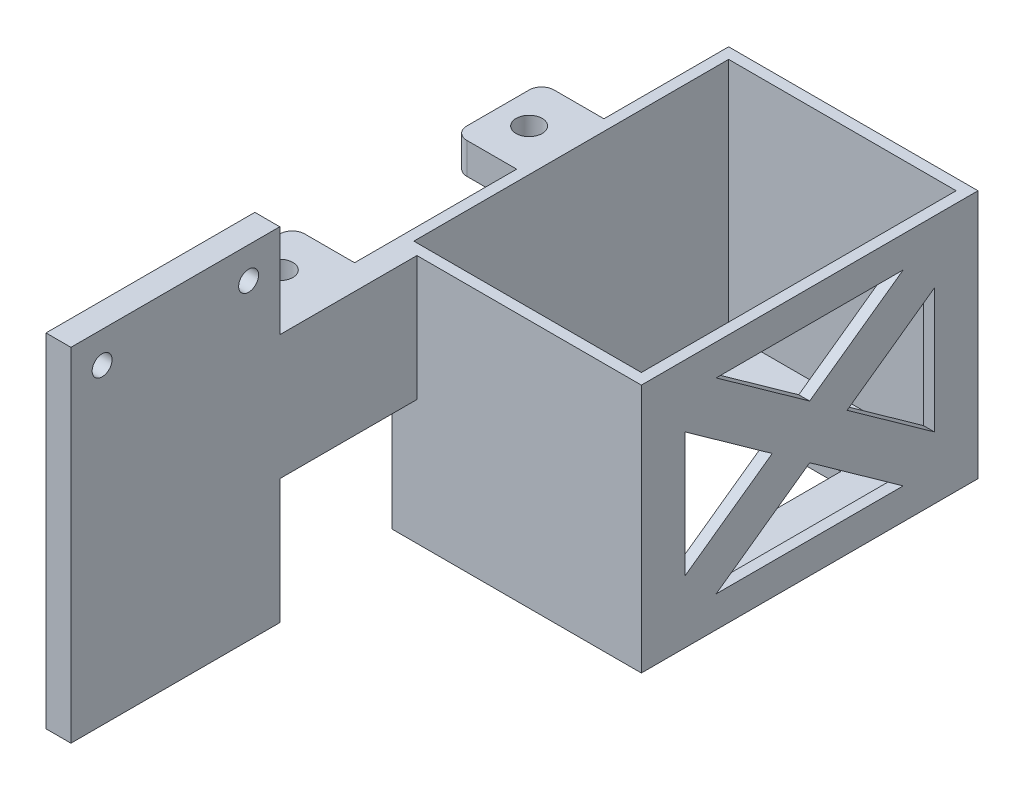
SolidWorks part; units mm, degrees
ref_plane "Front Plane" through (0, 0, 0) normal (0, 0, 1) x (1, 0, 0)
ref_plane "Top Plane" through (0, 0, 0) normal (0, 1, 0) x (1, 0, 0)
ref_plane "Right Plane" through (0, 0, 0) normal (1, 0, 0) x (0, 0, -1)
sketch "Sketch1" plane through (0, 0, 0) normal (0, 1, 0) x (1, 0, 0)
  line L1 (109.4484, -179.3604) -> (119.4484, -179.3604)
  line L2 (109.4484, -179.3604) -> (109.4484, -165.3604)
  line L3 (109.4484, -165.3604) -> (119.4484, -165.3604)
  line L4 (119.4484, -179.3604) -> (119.4484, -165.3604)
  line L5 (109.4484, -179.3604) -> (119.4484, -165.3604) construction
  line L6 (109.4484, -165.3604) -> (119.4484, -179.3604) construction
  line L8 (109.4484, -125.3604) -> (119.4484, -125.3604)
  line L9 (109.4484, -125.3604) -> (109.4484, -139.3604)
  line L10 (109.4484, -139.3604) -> (119.4484, -139.3604)
  line L11 (119.4484, -125.3604) -> (119.4484, -139.3604)
  line L12 (109.4484, -125.3604) -> (119.4484, -139.3604) construction
  line L13 (109.4484, -139.3604) -> (119.4484, -125.3604) construction
  circle A0 centre (114.4484, -172.3604) radius 2.1
  circle A1 centre (114.4484, -132.3604) radius 2.1
  point P0 (114.4484, -172.3604)
  point P8 (114.4484, -132.3604)
  dimension "D1" = 7
  dimension "D2" = 14
sketch "Sketch2" plane through (0, 0, 0) normal (0, 1, 0) x (1, 0, 0)
  line L1 (109.4484, -125.3604) -> (119.4484, -125.3604)
  line L2 (109.4484, -125.3604) -> (109.4484, -139.3604)
  line L3 (109.4484, -139.3604) -> (119.4484, -139.3604)
  line L4 (119.4484, -125.3604) -> (119.4484, -139.3604)
  line L5 (109.4484, -165.3604) -> (119.4484, -165.3604)
  line L6 (109.4484, -165.3604) -> (109.4484, -179.3604)
  line L7 (109.4484, -179.3604) -> (119.4484, -179.3604)
  line L8 (119.4484, -165.3604) -> (119.4484, -179.3604)
  circle A0 centre (114.4484, -132.3604) radius 2.1
  circle A1 centre (114.4484, -172.3604) radius 2.1
extrude "Boss-Extrude1" add sketch "Sketch2" along normal blind 5 contours L6 L5 L8 L7 | L2 L1 L4 L3 | A1 | A0
sketch "Sketch3" plane through (119.4484, 0, 0) normal (1, 0, 0) x (0, 0, -1)
  line L0 (-179.3604, 5) -> (-125.3604, 5) construction
  line L1 (-107.8604, 5) -> (-107.8604, -34)
  line L2 (-107.8604, 5) -> (-196.8604, 5)
  line L3 (-152.3604, 5) -> (-152.3604, -34)
  line L4 (-107.8604, -34) -> (-196.8604, -34)
  line L5 (-196.8604, 5) -> (-196.8604, -34)
  line M6 (-179.3604, 0) -> (-165.3604, 0)
  line M7 (-165.3604, 0) -> (-165.3604, 5)
  line M8 (-165.3604, 5) -> (-179.3604, 5)
  line M9 (-179.3604, 5) -> (-179.3604, 0)
  dimension "D1" = 39
  dimension "D2" = 44.5
extrude "Boss-Extrude2" add sketch "Sketch3" along normal blind 2 contours L2 L5 L4 L3 M7 M6 M9 | L4 L1 L2 L3 | M9 M6 M7 M8
sketch "Sketch4" plane through (121.4484, 0, 0) normal (1, 0, 0) x (0, 0, -1)
  line L0 (-107.8604, -34) -> (-196.8604, -34) construction
  line L1 (-196.8604, 5) -> (-194.8604, 5)
  line L2 (-196.8604, 5) -> (-196.8604, -34)
  line L3 (-196.8604, -34) -> (-194.8604, -34)
  line L4 (-194.8604, 5) -> (-194.8604, -34)
  line L5 (-152.3604, 5) -> (-152.3604, -34) construction
  line L6 (-107.8604, 5) -> (-196.8604, 5) construction
  line L7 (-107.8604, -34) -> (-109.8604, -34)
  line L8 (-109.8604, 5) -> (-109.8604, -34)
  line L9 (-107.8604, 5) -> (-109.8604, 5)
  line L10 (-107.8604, 5) -> (-107.8604, -34)
  line L13 (-194.8604, 5) -> (-194.8604, 3)
  line L15 (-109.8604, 5) -> (-109.8604, 3)
  line L16 (-194.8604, -34) -> (-109.8604, -34)
  line L17 (-194.8604, -34) -> (-194.8604, -32)
  line L18 (-194.8604, -32) -> (-109.8604, -32)
  line L19 (-109.8604, -34) -> (-109.8604, -32)
  line M6 (-107.8604, -34) -> (-107.8604, 5)
  line M7 (-107.8604, 5) -> (-196.8604, 5)
  line M8 (-196.8604, 5) -> (-196.8604, -34)
  line M9 (-196.8604, -34) -> (-107.8604, -34)
  dimension "D1" = 2
  dimension "D2" = 2
  dimension "D3" = 2
extrude "Boss-Extrude4" add sketch "Sketch4" along normal blind 32 contours L5 L18 L4 M9 | L18 L5 L16 L8 | L8 M7 M9 M6 | L4 M7 M8 M9
sketch "Sketch5" plane through (0, -32, 0) normal (0, 1, 0) x (1, 0, 0)
  line L0 (153.4484, -194.8604) -> (121.4484, -194.8604) construction
  line L1 (153.4484, -109.8604) -> (151.4484, -109.8604)
  line L2 (153.4484, -109.8604) -> (153.4484, -194.8604)
  line L3 (153.4484, -194.8604) -> (151.4484, -194.8604)
  line L4 (151.4484, -109.8604) -> (151.4484, -194.8604)
  dimension "D1" = 2
extrude "Boss-Extrude5" add sketch "Sketch5" along normal up to surface (37 mm away) up to face at (125.6984, 5, 152.3604)
sketch "Sketch6" plane through (0, 0, 196.8604) normal (0, 0, 1) x (1, 0, 0)
  line L0 (153.4484, 5) -> (119.4484, 5) construction
  line L1 (129.4484, 5) -> (143.4484, 5)
  line L2 (129.4484, 5) -> (129.4484, -25)
  line L3 (129.4484, -25) -> (143.4484, -25)
  line L4 (143.4484, 5) -> (143.4484, -25)
  line L5 (153.4484, 5) -> (153.4484, -34) construction
  line L6 (119.4484, 5) -> (119.4484, -34) construction
  dimension "D1" = 10
  dimension "D2" = 10
  dimension "D3" = 30
extrude "Cut-Extrude1" cut sketch "Sketch6" against normal blind 200
sketch "Sketch7" plane through (153.4484, 0, 0) normal (1, 0, 0) x (0, 0, -1)
  line L0 (-196.8604, -14.5) -> (-107.8604, -14.5) construction
  line L1 (-196.8604, 5) -> (-196.8604, -34) construction
  line L2 (-107.8604, -34) -> (-107.8604, 5) construction
  line L4 (-189.3604, -24.5) -> (-169.3604, -24.5)
  line L5 (-189.3604, -24.5) -> (-189.3604, -4.5)
  line L6 (-189.3604, -4.5) -> (-169.3604, -4.5)
  line L7 (-169.3604, -24.5) -> (-169.3604, -4.5)
  line L8 (-189.3604, -24.5) -> (-169.3604, -4.5) construction
  line L9 (-189.3604, -4.5) -> (-169.3604, -24.5) construction
  line L10 (-162.3604, -24.5) -> (-142.3604, -24.5)
  line L11 (-162.3604, -24.5) -> (-162.3604, -4.5)
  line L12 (-162.3604, -4.5) -> (-142.3604, -4.5)
  line L13 (-142.3604, -24.5) -> (-142.3604, -4.5)
  line L14 (-162.3604, -24.5) -> (-142.3604, -4.5) construction
  line L15 (-162.3604, -4.5) -> (-142.3604, -24.5) construction
  line L16 (-135.3604, -24.5) -> (-115.3604, -24.5)
  line L17 (-135.3604, -24.5) -> (-135.3604, -4.5)
  line L18 (-135.3604, -4.5) -> (-115.3604, -4.5)
  line L19 (-115.3604, -24.5) -> (-115.3604, -4.5)
  line L20 (-135.3604, -24.5) -> (-115.3604, -4.5) construction
  line L21 (-135.3604, -4.5) -> (-115.3604, -24.5) construction
  point P6 (-179.3604, -14.5)
  point P11 (-152.3604, -14.5)
  point P16 (-125.3604, -14.5)
  dimension "D1" = 7
  dimension "D2" = 20
  dimension "D3" = 20
  dimension "D4" = 20
  dimension "D5" = 20
  dimension "D6" = 20
  dimension "D7" = 20
  dimension "D8" = 7.5
extrude "Cut-Extrude2" cut sketch "Sketch7" against normal blind 16
fillet "Fillet1" radius 2 4 edges at (109.4484, 2.5, 125.3604) (109.4484, 2.5, 139.3604) (109.4484, 2.5, 165.3604) (109.4484, 2.5, 179.3604)
sketch "Sketch8" plane through (153.4484, 0, 0) normal (1, 0, 0) x (0, 0, -1)
  line L1 (-200.7189, -38.4244) -> (-104.7996, -38.4244)
  line L2 (-200.7189, -38.4244) -> (-200.7189, 8.239)
  line L3 (-200.7189, 8.239) -> (-104.7996, 8.239)
  line L4 (-104.7996, -38.4244) -> (-104.7996, 8.239)
  line L5 (-200.7189, -38.4244) -> (-104.7996, 8.239) construction
  line L6 (-200.7189, 8.239) -> (-104.7996, -38.4244) construction
  point P0 (-152.7592, -15.0927)
extrude "Cut-Extrude4" cut sketch "Sketch8" against normal up to surface (34 mm away) up to face at (119.4484, -3.1667, 152.3604)
sketch "Sketch9" plane through (119.4484, 0, 0) normal (1, 0, 0) x (0, 0, -1)
  line L0 (-132.3604, 5) -> (-132.3604, -35) construction
  line L1 (-125.3604, 5) -> (-139.3604, 5) construction
  line L2 (-157.3604, -35) -> (-157.3604, 5)
  line L3 (-157.3604, -35) -> (-107.3604, -35)
  line L4 (-132.3604, -35) -> (-132.3604, 5)
  line L5 (-157.3604, 5) -> (-107.3604, 5)
  line L6 (-107.3604, -35) -> (-107.3604, 5)
  line M7 (-139.3604, 5) -> (-139.3604, 0)
  line M8 (-139.3604, 0) -> (-125.3604, 0)
  line M9 (-125.3604, 0) -> (-125.3604, 5)
  line M10 (-125.3604, 5) -> (-139.3604, 5)
  dimension "D1" = 40
  dimension "D2" = 25
extrude "Boss-Extrude6" add sketch "Sketch9" along normal blind 2 contours L3 L6 L5 L4 M9 M8 | L5 L2 L3 L4 M8 M7 | L4 M8 M10 M7 | L4 M8 M9 M10
sketch "Sketch11" plane through (121.4484, 0, 0) normal (1, 0, 0) x (0, 0, -1)
  line L1 (-157.3604, 5) -> (-159.3604, 5)
  line L2 (-157.3604, 5) -> (-157.3604, -35)
  line L3 (-157.3604, -35) -> (-159.3604, -35)
  line L4 (-159.3604, 5) -> (-159.3604, -35)
  line L5 (-107.3604, 5) -> (-105.3604, 5)
  line L6 (-107.3604, 5) -> (-107.3604, -35)
  line L7 (-107.3604, -35) -> (-105.3604, -35)
  line L8 (-105.3604, 5) -> (-105.3604, -35)
  line L9 (-157.3604, -35) -> (-107.3604, -35)
  line L10 (-157.3604, -35) -> (-157.3604, -33)
  line L11 (-157.3604, -33) -> (-107.3604, -33)
  line L12 (-107.3604, -35) -> (-107.3604, -33)
  line M4 (-157.3604, 5) -> (-157.3604, -35)
  line M6 (-107.3604, -35) -> (-107.3604, 5)
  dimension "D1" = 2
  dimension "D2" = 2
  dimension "D3" = 2
extrude "Boss-Extrude9" add sketch "Sketch11" along normal blind 36 separate body contours L1 L4 L3 L2 M4 | L8 L5 L6 L7 M6
sketch "Sketch12" plane through (121.4484, 0, 0) normal (1, 0, 0) x (0, 0, -1)
  line L0 (-107.3604, -35) -> (-107.3604, 5) construction
  line L1 (-157.3604, -35) -> (-107.3604, -35)
  line L2 (-157.3604, -35) -> (-157.3604, -33)
  line L3 (-157.3604, -33) -> (-107.3604, -33)
  line L4 (-107.3604, -35) -> (-107.3604, -33)
  dimension "D1" = 2
extrude "Cut-Extrude5" cut sketch "Sketch12" against normal blind 36
sketch "Sketch13" plane through (121.4484, 0, 0) normal (1, 0, 0) x (0, 0, -1)
  line L1 (-157.3604, -33) -> (-107.3604, -33)
  line L2 (-157.3604, -33) -> (-157.3604, -35)
  line L3 (-157.3604, -35) -> (-107.3604, -35)
  line L4 (-107.3604, -33) -> (-107.3604, -35)
extrude "Boss-Extrude11" add sketch "Sketch13" along normal blind 36
sketch "Sketch14" plane through (121.4484, 0, 0) normal (-1, 0, 0) x (0, 0, 1)
  line L0 (107.3604, 5) -> (105.3604, 5)
  line L1 (105.3604, 5) -> (105.3604, -35)
  line L2 (105.3604, -35) -> (159.3604, -35)
  line L3 (159.3604, -35) -> (159.3604, 5)
  line L4 (159.3604, 5) -> (157.3604, 5)
  line L5 (157.3604, 5) -> (157.3604, -33)
  line L6 (157.3604, -33) -> (107.3604, -33)
  line L7 (107.3604, -33) -> (107.3604, 5)
extrude "Boss-Extrude12" add sketch "Sketch14" along normal up to surface (2 mm away) up to face at (119.4484, -5.75, 132.3604)
sketch "Sketch15" plane through (157.4484, 0, 0) normal (1, 0, 0) x (0, 0, -1)
  line L1 (-159.3604, 5) -> (-105.3604, 5)
  line L2 (-159.3604, 5) -> (-159.3604, -35)
  line L3 (-159.3604, -35) -> (-105.3604, -35)
  line L4 (-105.3604, 5) -> (-105.3604, -35)
extrude "Boss-Extrude13" add sketch "Sketch15" along normal blind 2
sketch "Sketch16" plane through (159.4484, 0, 0) normal (1, 0, 0) x (0, 0, -1)
  line L0 (-132.3604, 5) -> (-132.3604, -35) construction
  line L1 (-105.3604, 5) -> (-159.3604, 5) construction
  line L2 (-159.3604, -35) -> (-105.3604, -35) construction
  line L3 (-159.3604, -15) -> (-105.3604, -15) construction
  line L4 (-159.3604, 5) -> (-159.3604, -35) construction
  line L5 (-105.3604, -35) -> (-105.3604, 5) construction
  line L6 (-152.3604, -5) -> (-117.3604, -30)
  line L7 (-152.3604, -30) -> (-112.3604, -30)
  line L8 (-152.3604, -30) -> (-152.3604, 0)
  line L9 (-152.3604, 0) -> (-112.3604, 0)
  line L10 (-112.3604, -30) -> (-112.3604, 0)
  line L11 (-152.3604, -30) -> (-112.3604, 0) construction
  line L12 (-152.3604, 0) -> (-112.3604, -30) construction
  line L13 (-147.3604, 0) -> (-112.3604, -25)
  line L14 (-152.3604, -25) -> (-117.3604, 0)
  line L15 (-147.3604, -30) -> (-112.3604, -5)
  point P12 (-132.3604, -15)
  dimension "D1" = 30
  dimension "40" = 40
  dimension "D2" = 5
  dimension "D3" = 5
  dimension "D4" = 5
  dimension "D5" = 5
  dimension "D6" = 5
  dimension "D7" = 5
  dimension "D8" = 5
  dimension "D9" = 5
extrude "Cut-Extrude6" cut sketch "Sketch16" against normal blind 2 contours L8 L14 L6 | L13 L14 L9 | L15 L13 L10 | L15 L7 L6
sketch "Sketch17" plane through (119.4484, 0, 0) normal (1, 0, 0) x (0, 0, -1)
  line L1 (-159.3604, 5) -> (-214.3604, 5)
  line L2 (-159.3604, 5) -> (-159.3604, -32)
  line L3 (-159.3604, -32) -> (-214.3604, -32)
  line L4 (-214.3604, 5) -> (-214.3604, -32)
  dimension "D1" = 55
  dimension "D2" = 37
extrude "Boss-Extrude14" add sketch "Sketch17" along normal blind 4
sketch "Sketch18" plane through (123.4484, 0, 0) normal (1, 0, 0) x (0, 0, -1)
  line L0 (-214.3604, -13.5) -> (-159.3604, -13.5) construction
  line L3 (-186.8604, 5) -> (-186.8604, -33.1525) construction
  line L8 (-214.3604, 5) -> (-214.3604, -32) construction
  line L9 (-159.3604, -32) -> (-159.3604, 5) construction
  circle A0 centre (-209.3604, -1.75) radius 1.6
  circle A1 centre (-209.3604, -25.25) radius 1.6
  circle A4 centre (-164.3604, -25.25) radius 1.6
  circle A5 centre (-164.3604, -1.75) radius 1.6
  point P6 (-200.6104, -13.5)
  dimension "D2" = 3.2
  dimension "D3" = 3.2
  dimension "D4" = 22.5
  dimension "D5" = 11.75
  dimension "D6" = 11.75
  dimension "D1" = 22.5
extrude "Cut-Extrude7" cut sketch "Sketch18" against normal blind 11
sketch "Sketch19" plane through (119.4484, 0, 0) normal (-1, 0, 0) x (0, 0, 1)
  circle A0 centre (164.3604, -1.75) radius 1.6
extrude "Boss-Extrude15" add sketch "Sketch19" against normal up to surface (4 mm away) up to face at (123.4484, -25.25, 207.7604)
sketch "Sketch20" plane through (119.4484, 0, 0) normal (-1, 0, 0) x (0, 0, 1)
  circle A0 centre (209.3604, -1.75) radius 3.6
  circle A1 centre (209.3604, -25.25) radius 3.6
  circle A2 centre (164.3604, -25.25) radius 3.6
  dimension "D1" = 7.2
  dimension "D2" = 7.2
  dimension "D3" = 7.2
extrude "Cut-Extrude8" cut sketch "Sketch20" against normal blind 2.2 contours A0 | A1 | A2
sketch "Sketch21" plane through (123.4484, 0, 0) normal (1, 0, 0) x (0, 0, -1)
  line L1 (-159.3604, -32) -> (-216.2773, -32)
  line L2 (-159.3604, -32) -> (-159.3604, 7.408)
  line L3 (-159.3604, 7.408) -> (-216.2773, 7.408)
  line L4 (-216.2773, -32) -> (-216.2773, 7.408)
extrude "Cut-Extrude9" cut sketch "Sketch21" against normal up to surface (4 mm away) up to face at (119.4484, -1.75, 212.9604)
sketch "Sketch22" plane through (119.4484, 0, 0) normal (1, 0, 0) x (0, 0, -1)
  line L0 (-189.3604, 20) -> (-189.3604, -7.5)
  line L1 (-189.3604, 20) -> (-226.8604, 20)
  line L4 (-226.8604, 20) -> (-226.8604, -7.5)
  line L7 (-208.1104, 20) -> (-208.1104, -7.5) construction
  line L8 (-208.1104, -7.5) -> (-189.3604, -7.5) construction
  line L9 (-226.8604, -7.5) -> (-189.3604, -7.5)
  circle A0 centre (-219.8604, 15) radius 1.6
  circle A1 centre (-196.3604, 15) radius 1.6
  dimension "D4" = 3.2
  dimension "D5" = 3.2
  dimension "D6" = 11.75
  dimension "D7" = 11.75
  dimension "D8" = 22.5
  dimension "D9" = 22.5
  dimension "D3" = 37.5
extrude "Boss-Extrude16" add sketch "Sketch22" along normal blind 2 separate body
sketch "Sketch23" plane through (119.4484, 0, 0) normal (1, 0, 0) x (0, 0, -1)
  line L1 (-159.3604, 5) -> (-189.3604, 5)
  line L2 (-159.3604, 5) -> (-159.3604, -7.5)
  line L3 (-159.3604, -7.5) -> (-189.3604, -7.5)
  line L4 (-189.3604, 5) -> (-189.3604, -7.5)
extrude "Boss-Extrude17" add sketch "Sketch23" along normal blind 2
sketch "Sketch25" plane through (0, -35, 0) normal (0, -1, 0) x (-1, 0, 0)
  line L0 (-139.4484, -159.3604) -> (-139.4484, -105.3604) construction
  line L1 (-119.4484, -159.3604) -> (-159.4484, -159.3604) construction
  line L2 (-119.4484, -105.3604) -> (-159.4484, -105.3604) construction
  line L4 (-129.4484, -117.3604) -> (-149.4484, -117.3604)
  line L5 (-129.4484, -117.3604) -> (-129.4484, -147.3604)
  line L6 (-129.4484, -147.3604) -> (-149.4484, -147.3604)
  line L7 (-149.4484, -117.3604) -> (-149.4484, -147.3604)
  line L8 (-129.4484, -117.3604) -> (-149.4484, -147.3604) construction
  line L9 (-129.4484, -147.3604) -> (-149.4484, -117.3604) construction
  point P6 (-139.4484, -132.3604)
  dimension "D1" = 20
  dimension "D2" = 30
extrude "Cut-Extrude10" cut sketch "Sketch25" against normal blind 15
sketch "Sketch26" plane through (121.4484, 0, 0) normal (1, 0, 0) x (0, 0, -1)
  line L1 (-189.3604, 20) -> (-226.8604, 20)
  line L2 (-189.3604, 20) -> (-189.3604, 5)
  line L4 (-226.8604, 20) -> (-226.8604, -7.5)
  line L5 (-189.3604, 5) -> (-159.3604, 5)
  line L7 (-189.3604, -7.5) -> (-159.3604, -7.5)
  line L8 (-159.3604, 5) -> (-159.3604, -7.5)
  line L9 (-189.3604, -35) -> (-226.8604, -35)
  line L10 (-159.3604, -35) -> (-159.3604, -7.5)
  line L11 (-159.3604, -7.5) -> (-189.3604, -7.5)
  line L12 (-226.8604, -35) -> (-226.8604, -7.5)
  line L13 (-189.3604, -7.5) -> (-159.3604, -7.5)
  line L14 (-189.3604, -7.5) -> (-189.3604, -35)
  line L16 (-159.3604, -7.5) -> (-159.3604, -35)
  circle A0 centre (-219.8604, 15) radius 1.6
  circle A1 centre (-196.3604, 15) radius 1.6
  line M1 (-159.3604, -7.5) -> (-159.3604, 5)
  line M2 (-159.3604, 5) -> (-189.3604, 5)
  line M3 (-189.3604, 5) -> (-189.3604, 20)
  line M4 (-189.3604, 20) -> (-226.8604, 20)
  line M5 (-226.8604, 20) -> (-226.8604, -7.5)
  line M6 (-226.8604, -7.5) -> (-159.3604, -7.5)
  circle M7 centre (-219.8604, 15) radius 1.6
  circle M8 centre (-196.3604, 15) radius 1.6
extrude "Boss-Extrude18" add sketch "Sketch26" along normal blind 2 contours M6 M1 M2 M3 M4 M5 M7 M8 | L14 L12 L9 M6
sketch "Sketch27" plane through (121.4484, 0, 0) normal (-1, 0, 0) x (0, 0, 1)
  line L1 (189.3604, -7.5) -> (226.8604, -7.5)
  line L2 (189.3604, -7.5) -> (189.3604, -35)
  line L3 (189.3604, -35) -> (226.8604, -35)
  line L4 (226.8604, -7.5) -> (226.8604, -35)
extrude "Boss-Extrude19" add sketch "Sketch27" along normal up to surface (2 mm away) up to face at (119.4484, -0.9375, 161.2979)
sketch "Sketch28" plane through (0, 5, 0) normal (0, 1, 0) x (1, 0, 0)
  line L0 (139.4484, -107.3604) -> (139.4484, -157.3604) construction
  line L1 (157.4484, -107.3604) -> (121.4484, -107.3604) construction
  line L2 (157.4484, -157.3604) -> (121.4484, -157.3604) construction
  line L4 (121.1984, -157.6104) -> (157.6984, -157.6104)
  line L5 (121.1984, -157.6104) -> (121.1984, -107.1104)
  line L6 (121.1984, -107.1104) -> (157.6984, -107.1104)
  line L7 (157.6984, -157.6104) -> (157.6984, -107.1104)
  line L8 (121.1984, -157.6104) -> (157.6984, -107.1104) construction
  line L9 (121.1984, -107.1104) -> (157.6984, -157.6104) construction
  point P6 (139.4484, -132.3604)
  dimension "D1" = 50.5
  dimension "D2" = 36.5
extrude "Cut-Extrude11" cut sketch "Sketch28" against normal up to surface (38 mm away) up to face at (139.4484, -33, 132.3604)
sketch "Sketch29" plane through (123.4484, 0, 0) normal (1, 0, 0) x (0, 0, -1)
  line L0 (-219.8604, 15) -> (-209.8604, 15) construction
  line L1 (-196.3604, 15) -> (-186.3604, 15)
  line L3 (-189.3604, 20) -> (-226.8604, 20) construction
  line L4 (-214.8604, 20) -> (-181.3604, 20)
  line L5 (-214.8604, 20) -> (-214.8604, -35)
  line L6 (-214.8604, -35) -> (-181.3604, -35)
  line L7 (-181.3604, 20) -> (-181.3604, -35)
  circle A0 centre (-186.3604, 15) radius 1.6
  circle A1 centre (-209.8604, 15) radius 1.6
  dimension "D3" = 3.2
  dimension "D4" = 3.2
  dimension "D6" = 5
  dimension "D1" = 10
  dimension "D2" = 10
  dimension "D5" = 5
extrude "Boss-Extrude20" add sketch "Sketch29" against normal up to surface (4 mm away)
sketch "Sketch30" plane through (123.4484, 0, 0) normal (1, 0, 0) x (0, 0, -1)
  line L1 (-226.8604, 20) -> (-214.8604, 20)
  line L2 (-226.8604, 20) -> (-226.8604, -35)
  line L3 (-226.8604, -35) -> (-214.8604, -35)
  line L4 (-214.8604, 20) -> (-214.8604, -35)
extrude "Cut-Extrude12" cut sketch "Sketch30" against normal up to surface (4 mm away) up to face at (119.4484, -4.7222, 162.6382)
sketch "Sketch31" plane through (123.4484, 0, 0) normal (1, 0, 0) x (0, 0, -1)
  circle A0 centre (-209.8604, 15) radius 1.6
extrude "Cut-Extrude13" cut sketch "Sketch31" against normal up to surface (4 mm away) contours A0 up to face at (119.4484, -4.7222, 161.3049)
sketch "Sketch32" plane through (123.4484, 0, 0) normal (1, 0, 0) x (0, 0, -1)
  line L0 (-159.3604, 5) -> (-159.3604, -35) construction
  line L1 (-181.3604, 5) -> (-159.3604, 5)
  line L2 (-181.3604, 5) -> (-181.3604, -15)
  line L3 (-181.3604, -15) -> (-159.3604, -15)
  line L4 (-159.3604, 5) -> (-159.3604, -15)
  dimension "D1" = 20
extrude "Boss-Extrude21" add sketch "Sketch32" against normal up to surface (4 mm away) up to face at (119.4484, 15, 211.4604)
